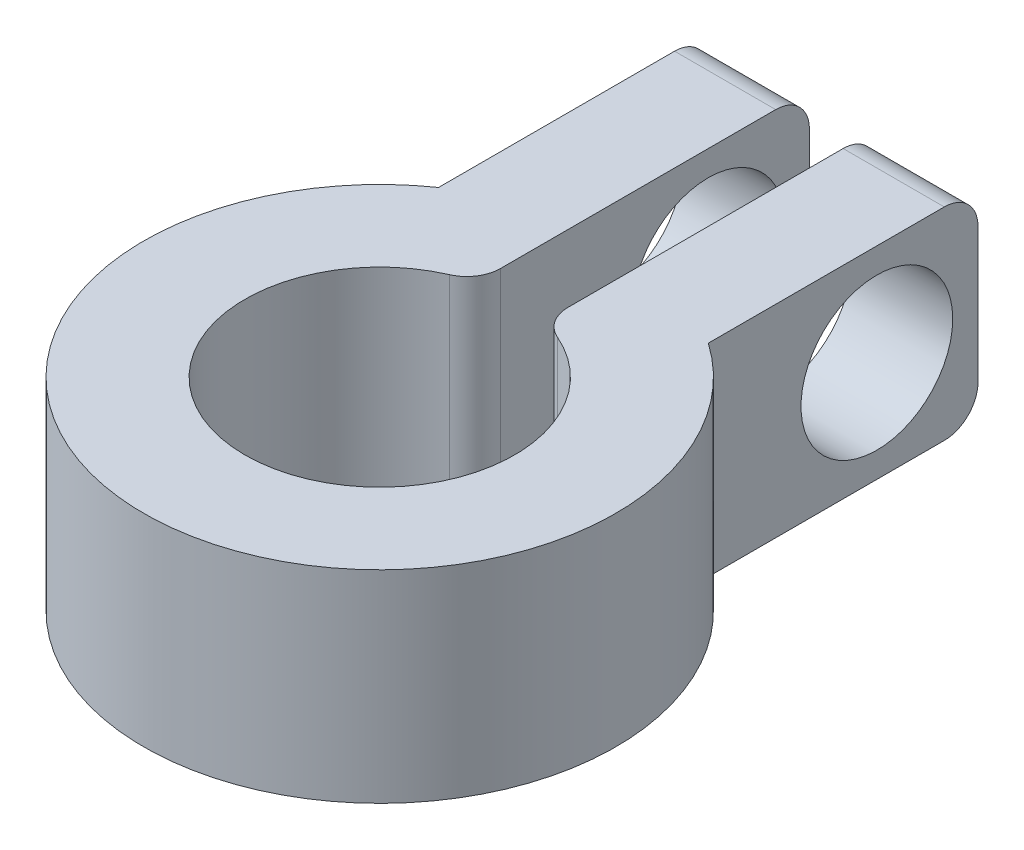
SolidWorks part; units mm, degrees
ref_plane "Front Plane" through (0, 0, 0) normal (0, 0, 1) x (1, 0, 0)
ref_plane "Top Plane" through (0, 0, 0) normal (0, 1, 0) x (1, 0, 0)
ref_plane "Right Plane" through (0, 0, 0) normal (1, 0, 0) x (0, 0, -1)
sketch "Sketch2" plane through (0, 0, 0) normal (0, 1, 0) x (1, 0, 0)
  line L0 (-1, 3.873) -> (-1, 13.7446)
  line L1 (-1, 13.7446) -> (-4, 13.7446)
  line L2 (-4, 13.7446) -> (-4, 5.7446)
  line L3 (0, 0) -> (0, -4) construction
  line L4 (1, 3.873) -> (1, 13.7446)
  line L5 (1, 13.7446) -> (4, 13.7446)
  line L6 (4, 13.7446) -> (4, 5.7446)
  arc A0 (-1, 3.873) -> (1, 3.873) centre (0, 0) ccw
  arc A1 (-4, 5.7446) -> (4, 5.7446) centre (0, 0) ccw
  dimension "D1" = 8
  dimension "D2" = 14
  dimension "D3" = 3
  dimension "D4" = 1
  dimension "D5" = 8
extrude "Boss-Extrude1" add sketch "Sketch2" along normal blind 6
sketch "Sketch3" plane through (4, 0, 0) normal (1, 0, 0) x (0, 0, -1)
  line L0 (13.7446, 6) -> (13.7446, 0) construction
  line L1 (5.7446, 6) -> (13.7446, 6) construction
  circle A0 centre (10.7446, 3) radius 2.25
  circle A1 centre (10.7446, 3) radius 4 construction
  dimension "D1" = 4.5
  dimension "D3" = 8
  dimension "D2" = 3
  dimension "D4" = 3
extrude "Cut-Extrude1" cut sketch "Sketch3" against normal blind 10
fillet "Fillet1" radius 1 6 edges at (1, 3, -3.873) (-1, 3, -3.873) (-2.5, 6, -13.7446) (-2.5, 0, -13.7446) (2.5, 0, -13.7446) (2.5, 6, -13.7446)
